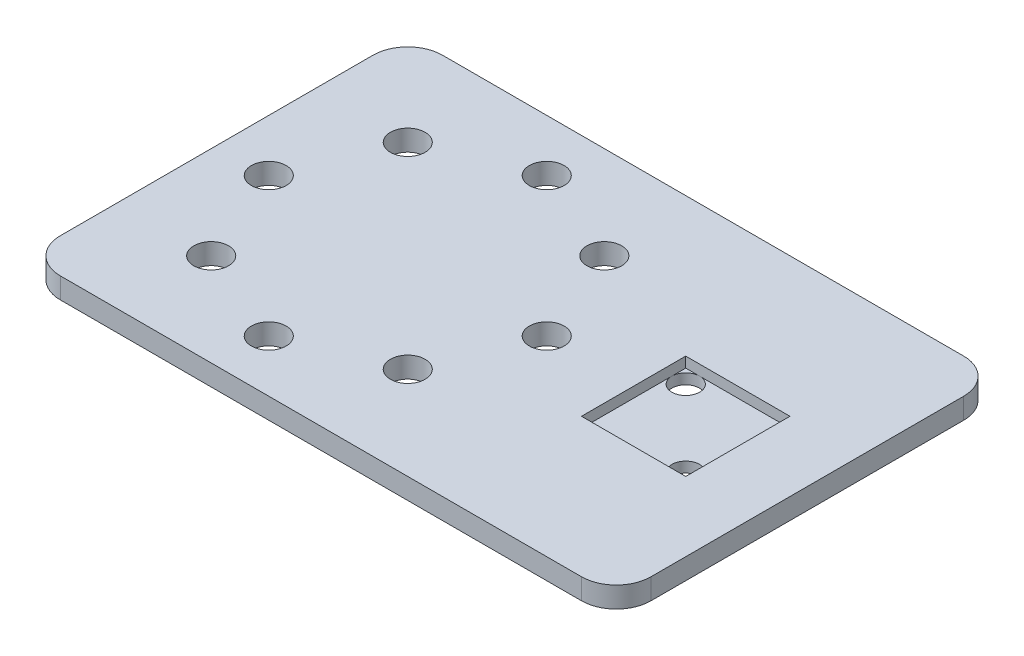
SolidWorks part; units mm, degrees
ref_plane "Front Plane" through (0, 0, 0) normal (0, 0, 1) x (1, 0, 0)
ref_plane "Top Plane" through (0, 0, 0) normal (0, 1, 0) x (1, 0, 0)
ref_plane "Right Plane" through (0, 0, 0) normal (1, 0, 0) x (0, 0, -1)
sketch "Sketch1" plane through (0, 0, 0) normal (0, 1, 0) x (1, 0, 0)
  line L0 (-37.5, -0.4333) -> (-15, -0.4333) construction
  line L5 (-15, -0.4333) -> (-35, -0.4333) construction
  line L6 (42.5, -27.9333) -> (-42.5, -27.9333)
  line L7 (32.5, -7.9333) -> (17.5, -7.9333)
  line L8 (32.5, -7.9333) -> (32.5, 7.0667)
  line L9 (32.5, 7.0667) -> (17.5, 7.0667)
  line L10 (17.5, -7.9333) -> (17.5, 7.0667)
  line L11 (32.5, -7.9333) -> (17.5, 7.0667) construction
  line L12 (32.5, 7.0667) -> (17.5, -7.9333) construction
  line L13 (42.5, -27.9333) -> (42.5, 27.0667)
  line L14 (42.5, 27.0667) -> (-42.5, 27.0667)
  line L15 (-42.5, -27.9333) -> (-42.5, 27.0667)
  circle A0 centre (-35, -0.4333) radius 2.5
  circle A1 centre (-29.1421, 13.7089) radius 2.5
  circle A2 centre (-15, 19.5667) radius 2.5
  circle A3 centre (-0.8579, 13.7089) radius 2.5
  circle A4 centre (5, -0.4333) radius 2.5
  circle A5 centre (-0.8579, -14.5754) radius 2.5
  circle A6 centre (-15, -20.4333) radius 2.5
  circle A7 centre (-29.1421, -14.5754) radius 2.5
  point P0 (0, 0)
  point P6 (25, -0.4333)
  dimension "D3" = 5
  dimension "D4" = 10
  dimension "D1" = 55
  dimension "D2" = 85
  dimension "D5" = 20
  dimension "D6" = 22.5
  dimension "D8" = 20
  dimension "D9" = 15
  dimension "D10" = 27.5
  dimension "D11" = 27.5
  dimension "D7" = 8
  dimension "D12" = 20
extrude "Boss-Extrude3" add sketch "Sketch1" along normal blind 3
fillet "Fillet2" radius 5 4 edges at (42.5, 1.5, -27.0667) (-42.5, 1.5, -27.0667) (-42.5, 1.5, 27.9333) (42.5, 1.5, 27.9333)
sketch "Sketch2" plane through (17.5, 0, 0) normal (1, 0, 0) x (0, 0, -1)
  line L0 (-7.9333, 3) -> (-7.9333, 0) construction
  line L1 (7.0667, 0) -> (-7.9333, 0)
  line L2 (7.0667, 0) -> (7.0667, 1.5)
  line L3 (7.0667, 1.5) -> (-7.9333, 1.5)
  line L4 (-7.9333, 0) -> (-7.9333, 1.5)
  dimension "D1" = 1.5
extrude "Boss-Extrude4" add sketch "Sketch2" along normal up to next
sketch "Sketch3" plane through (0, 1.5, 0) normal (0, 1, 0) x (1, 0, 0)
  line L0 (32.5, -7.9333) -> (32.5, 7.0667) construction
  line L6 (17.5, -7.9333) -> (32.5, -7.9333) construction
  line L7 (32.5, 7.0667) -> (17.5, 7.0667) construction
  line L8 (17.5, 7.0667) -> (17.5, -7.9333) construction
  circle A4 centre (19.5, 5.0667) radius 2
  circle A5 centre (30.5, -5.9333) radius 2
  dimension "D1" = 4
  dimension "D2" = 4
  dimension "D3" = 2
  dimension "D4" = 2
  dimension "D5" = 2
  dimension "D6" = 2
extrude "Cut-Extrude1" cut sketch "Sketch3" against normal blind 10 contours A5 | A4
